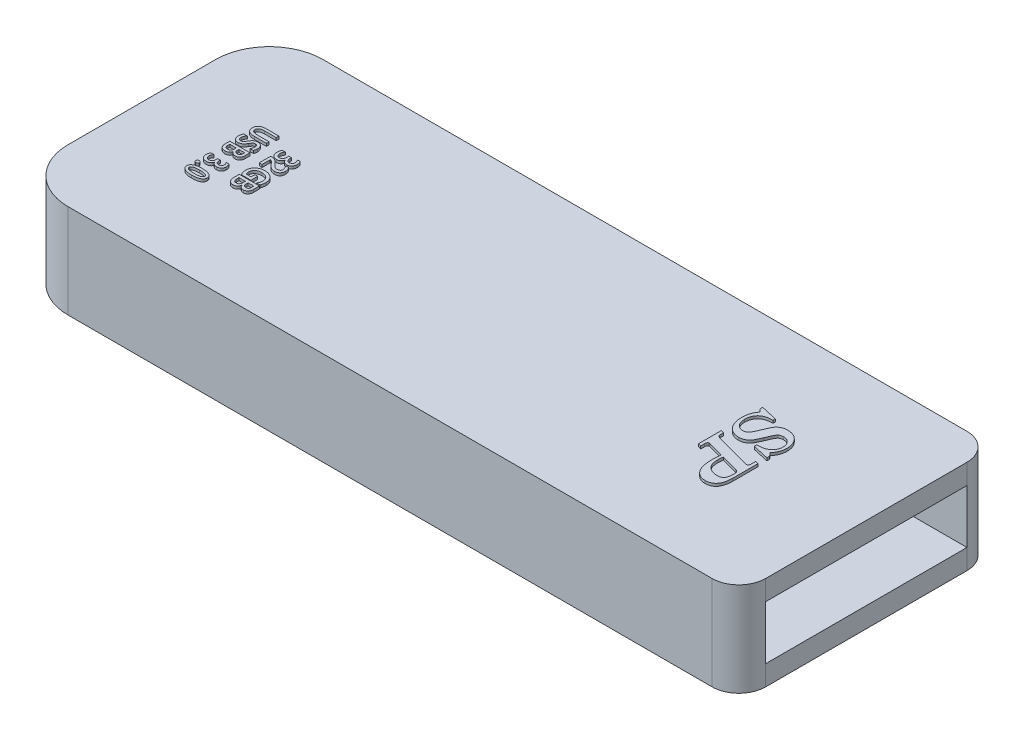
SolidWorks part; units mm, degrees
ref_plane "Front Plane" through (0, 0, 0) normal (0, 0, 1) x (1, 0, 0)
ref_plane "Top Plane" through (0, 0, 0) normal (0, 1, 0) x (1, 0, 0)
ref_plane "Right Plane" through (0, 0, 0) normal (1, 0, 0) x (0, 0, -1)
sketch "Sketch1" plane through (0, 0, 0) normal (0, 1, 0) x (1, 0, 0)
  line L1 (0, 0) -> (-50, 0)
  line L2 (0, 0) -> (0, 19)
  line L3 (0, 19) -> (-50, 19)
  line L4 (-54, 4) -> (-54, 15)
  arc A0 (-50, 0) -> (-54, 4) centre (-50, 4) cw
  arc A1 (-50, 19) -> (-54, 15) centre (-50, 15) ccw
  point P7 (-54, 0)
  point P10 (-54, 19)
  dimension "D3" = 4
  dimension "D1" = 19
  dimension "D2" = 54
extrude "Boss-Extrude1" add sketch "Sketch1" along normal blind 7
fillet "Fillet2" radius 2 2 edges at (0, 3.5, -19) (0, 3.5, 0)
ref_plane "Plane1" through (10, 0, 0) normal (1, 0, 0) x (0, 0, -1)
sketch "Sketch2" plane through (10, 0, 0) normal (1, 0, 0) x (0, 0, -1)
  line L0 (2, 5.5) -> (2, 1.5)
  line L1 (2, 7) -> (2, 0) construction
  line L2 (2, 1.5) -> (17, 1.5)
  line L3 (17, 0) -> (17, 7) construction
  line L4 (17, 1.5) -> (17, 5.5)
  line L5 (17, 5.5) -> (2, 5.5)
  line L6 (2, 7) -> (17, 7) construction
  line L7 (2, 0) -> (17, 0) construction
  dimension "D1" = 1.5
  dimension "D2" = 1.5
extrude "Cut-Extrude1" cut sketch "Sketch2" against normal blind 60
sketch "Sketch3" plane through (0, 0, 0) normal (0, -1, 0) x (1, 0, 0)
  line L0 (-50, 0) -> (-2, 0) construction
  line L1 (-37, -14) -> (-13, -14)
  line L2 (-37, -14) -> (-37, -5)
  line L3 (-37, -5) -> (-13, -5)
  line L4 (-13, -14) -> (-13, -5)
  line L5 (-37, -14) -> (-13, -5) construction
  line L6 (-37, -5) -> (-13, -14) construction
  line L8 (-54, -15) -> (-54, -4) construction
  point P0 (-25, -9.5)
  dimension "D1" = 9
  dimension "D2" = 24
  dimension "D3" = 5
  dimension "D4" = 17
extrude "Cut-Extrude2" cut sketch "Sketch3" against normal up to surface (5.5 mm away) up to face at (-25, 5.5, -9.5)
sketch "Sketch4" plane through (0, 7, 0) normal (0, 1, 0) x (1, 0, 0)
  line L0 (-2, 19) -> (-50, 19) construction
  line L1 (-7, 14) -> (-11, 14) construction
  line L2 (-7, 14) -> (-7, 5) construction
  line L3 (-7, 5) -> (-11, 5) construction
  line L4 (-11, 14) -> (-11, 5) construction
  line L5 (-50, 0) -> (-2, 0) construction
  line L6 (0, 2) -> (0, 17) construction
  text T0 "<b><i>SP</i></b>" font "Century Schoolbook" height 3.5
  dimension "D1" = 5
  dimension "D2" = 5
  dimension "D3" = 7
  dimension "D4" = 4
extrude "Boss-Extrude3" add sketch "Sketch4" along normal blind 0.2
sketch "Sketch6" plane through (0, 7, 0) normal (0, 1, 0) x (1, 0, 0)
  line L0 (-54, 15) -> (-54, 4) construction
  line L1 (-48, 14) -> (-43.0114, 14) construction
  line L2 (-48, 14) -> (-48, 5) construction
  line L3 (-48, 5) -> (-43.0114, 5) construction
  line L4 (-43.0114, 14) -> (-43.0114, 5) construction
  line L5 (-2, 19) -> (-50, 19) construction
  line L6 (-50, 0) -> (-2, 0) construction
  line L7 (0, 2) -> (0, 17) construction
  line L8 (-45.5057, 14) -> (-45.5057, 5) construction
  text T0 "<b>32 GB</b>" font "Yu Gothic UI" height 1.5
  text T1 "<b>USB 3.0</b>" font "Yu Gothic UI" height 1.5
  point P10 (-45.5057, 5)
  dimension "D1" = 6
  dimension "D2" = 5
  dimension "D3" = 5
  dimension "D4" = 43.0114
extrude "Boss-Extrude4" add sketch "Sketch6" along normal blind 0.2
